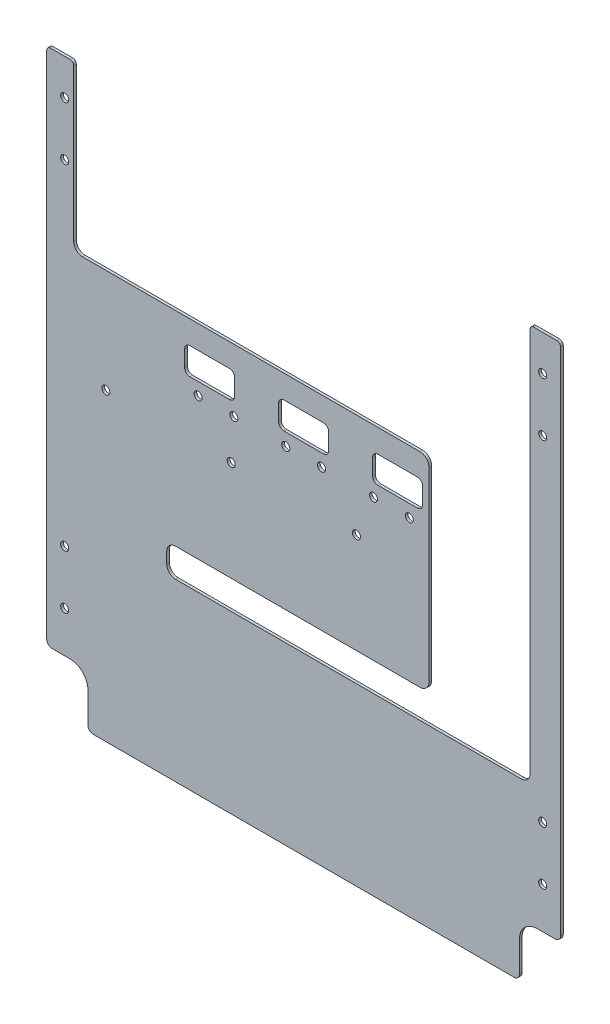
SolidWorks part; units mm, degrees
material "1023 Tôle d'acier au carbone (SS)"
ref_plane "Front" through (0, 0, 0) normal (0, 0, 1) x (1, 0, 0)
ref_plane "Top" through (0, 0, 0) normal (0, 1, 0) x (1, 0, 0)
ref_plane "Right" through (0, 0, 0) normal (1, 0, 0) x (0, 0, -1)
sketch "Esquisse1" plane through (0, 0, 0) normal (0, 0, 1) x (1, 0, 0)
  line L1 (0, 0) -> (287, 0)
  line L2 (0, 0) -> (0, 320)
  line L3 (0, 320) -> (287, 320)
  line L4 (287, 0) -> (287, 320)
  dimension "D1" = 287
  dimension "D2" = 320
extrude "Boss.-Extru.1" add sketch "Esquisse1" along normal blind 1.5
sketch "Esquisse2" plane through (0, 0, 1.5) normal (0, 0, 1) x (1, 0, 0)
  line L0 (143.5, 0) -> (143.5, 56.1801) construction
  line L1 (287, 0) -> (264, 0)
  line L2 (287, 0) -> (287, 30)
  line L3 (287, 30) -> (264, 30)
  line L4 (264, 0) -> (264, 30)
  line L5 (0, 0) -> (287, 0) construction
  line L6 (23, 0) -> (23, 30)
  line L7 (0, 30) -> (23, 30)
  line L8 (0, 0) -> (0, 30)
  line L9 (0, 0) -> (23, 0)
  dimension "D1" = 23
  dimension "D2" = 30
extrude "Enlèv. mat.-Extru.1" cut sketch "Esquisse2" against normal through all both and the other way through all
fillet "Congé1" radius 10 2 edges at (264, 30, 0.75) (23, 30, 0.75)
fillet "Congé2" radius 3 4 edges at (287, 30, 0.75) (0, 30, 0.75) (23, 0, 0.75) (264, 0, 0.75)
sketch "Esquisse3" plane through (0, 0, 1.5) normal (0, 0, 1) x (1, 0, 0)
  line L0 (287, 320) -> (0, 320) construction
  line L1 (73.5, 320) -> (213.5, 320)
  line L2 (73.5, 320) -> (73.5, 228)
  line L3 (73.5, 228) -> (213.5, 228)
  line L4 (213.5, 320) -> (213.5, 228)
  line L5 (143.5, 228) -> (143.5, 0) construction
  line L6 (26, 0) -> (261, 0) construction
  dimension "D1" = 140
  dimension "D2" = 92
extrude "Enlèv. mat.-Extru.2" cut sketch "Esquisse3" against normal through all both and the other way through all
sketch "Esquisse4" plane through (0, 0, 1.5) normal (0, 0, 1) x (1, 0, 0)
  line L0 (287, 320) -> (213.5, 320) construction
  line L1 (213.5, 320) -> (270, 320)
  line L2 (213.5, 320) -> (213.5, 98)
  line L3 (213.5, 98) -> (270, 98)
  line L4 (270, 320) -> (270, 98)
  line L5 (287, 33) -> (287, 320) construction
  line L6 (213.5, 320) -> (213.5, 228) construction
  line L7 (26, 0) -> (261, 0) construction
  dimension "D1" = 17
  dimension "D2" = 98
extrude "Enlèv. mat.-Extru.3" cut sketch "Esquisse4" against normal through all both and the other way through all
sketch "Esquisse5" plane through (0, 0, 1.5) normal (0, 0, 1) x (1, 0, 0)
  line L0 (73.5, 320) -> (0, 320) construction
  line L1 (73.5, 228) -> (15, 228)
  line L2 (73.5, 228) -> (73.5, 320)
  line L3 (73.5, 320) -> (15, 320)
  line L4 (15, 228) -> (15, 320)
  line L5 (0, 320) -> (0, 33) construction
  dimension "D1" = 15
extrude "Enlèv. mat.-Extru.4" cut sketch "Esquisse5" against normal through all both and the other way through all
sketch "Esquisse6" plane through (0, 0, 1.5) normal (0, 0, 1) x (1, 0, 0)
  line L0 (213.5, 98) -> (213.5, 228) construction
  line L1 (213.5, 98) -> (67, 98)
  line L2 (213.5, 98) -> (213.5, 114)
  line L3 (213.5, 114) -> (67, 114)
  line L4 (67, 98) -> (67, 114)
  line L5 (26, 0) -> (261, 0) construction
  line L6 (0, 320) -> (0, 33) construction
  dimension "D1" = 16
  dimension "D2" = 98
  dimension "D3" = 67
extrude "Enlèv. mat.-Extru.5" cut sketch "Esquisse6" against normal through all both and the other way through all
fillet "Congé3" radius 5 6 edges at (270, 98, 0.75) (67, 98, 0.75) (67, 114, 0.75) (213.5, 114, 0.75) (213.5, 228, 0.75) (15, 228, 0.75)
sketch "Esquisse7" plane through (0, 0, 1.5) normal (0, 0, 1) x (1, 0, 0)
  line L0 (277, 320) -> (277, 300) construction
  line L1 (287, 320) -> (270, 320) construction
  line L2 (270, 320) -> (270, 103) construction
  line L3 (277, 300) -> (277, 270) construction
  line L4 (143.5, 0) -> (143.5, 300) construction
  line L5 (26, 0) -> (261, 0) construction
  line L6 (10, 300) -> (10, 270) construction
  line L7 (10, 320) -> (10, 300) construction
  line L8 (0, 176.5) -> (287, 176.5) construction
  line L9 (0, 320) -> (0, 33) construction
  line L10 (287, 33) -> (287, 320) construction
  line L11 (277, 53) -> (277, 83) construction
  line L12 (277, 33) -> (277, 53) construction
  line L13 (10, 33) -> (10, 53) construction
  line L14 (10, 53) -> (10, 83) construction
  line L15 (33, 170) -> (0, 170) construction
  line L16 (33, 170) -> (103, 170) construction
  line L17 (103, 170) -> (103, 182.3786) construction
  circle A0 centre (277, 300) radius 2.25
  circle A1 centre (277, 270) radius 2.25
  circle A2 centre (10, 270) radius 2.25
  circle A3 centre (10, 300) radius 2.25
  circle A4 centre (277, 83) radius 2.25
  circle A5 centre (277, 53) radius 2.25
  circle A6 centre (10, 53) radius 2.25
  circle A7 centre (10, 83) radius 2.25
  circle A8 centre (33, 170) radius 2.25
  circle A9 centre (103, 170) radius 2.25
  circle A10 centre (173, 170) radius 2.25
  dimension "D2" = 4.5
  dimension "D4" = 30
  dimension "D6" = 33
  dimension "D1" = 7
  dimension "D3" = 20
  dimension "D5" = 70
  dimension "D7" = 170
extrude "Enlèv. mat.-Extru.6" cut sketch "Esquisse7" against normal through all both and the other way through all
sketch "Esquisse8" plane through (0, 0, 1.5) normal (0, 0, 1) x (1, 0, 0)
  line L0 (143.5, 0) -> (143.5, 158.346) construction
  line L1 (26, 0) -> (261, 0) construction
  line L2 (208.5, 228) -> (20, 228) construction
  line L3 (182.5, 193) -> (202.5, 193) construction
  line L4 (153.5, 193) -> (182.5, 193) construction
  line L5 (104.5, 193) -> (84.5, 193) construction
  circle A0 centre (133.5, 193) radius 2.25
  circle A1 centre (153.5, 193) radius 2.25
  circle A2 centre (182.5, 193) radius 2.25
  circle A3 centre (202.5, 193) radius 2.25
  circle A4 centre (84.5, 193) radius 2.25
  circle A5 centre (104.5, 193) radius 2.25
  dimension "D1" = 4.5
  dimension "D2" = 20
  dimension "D3" = 35
  dimension "D4" = 20
  dimension "D5" = 39
extrude "Enlèv. mat.-Extru.7" cut sketch "Esquisse8" against normal through all both and the other way through all
sketch "Esquisse9" plane through (0, 0, 1.5) normal (0, 0, 1) x (1, 0, 0)
  line L0 (133.5, 193) -> (153.5, 193) construction
  line L1 (129.5, 215) -> (157.5, 215)
  line L2 (129.5, 215) -> (129.5, 200)
  line L3 (129.5, 200) -> (157.5, 200)
  line L4 (157.5, 215) -> (157.5, 200)
  line L5 (143.5, 193) -> (143.5, 215) construction
  line L6 (153.5, 193) -> (169.75, 193) construction
  line L7 (169.75, 193) -> (169.75, 205) construction
  line L8 (182, 215) -> (182, 200)
  line L9 (210, 200) -> (182, 200)
  line L10 (210, 215) -> (210, 200)
  line L11 (210, 215) -> (182, 215)
  line L12 (182.5, 193) -> (182.5, 194.1597) construction
  line L13 (104.5, 193) -> (104.5, 194.1597) construction
  line L14 (77, 215) -> (105, 215)
  line L15 (77, 215) -> (77, 200)
  line L16 (77, 200) -> (105, 200)
  line L17 (105, 215) -> (105, 200)
  dimension "D1" = 28
  dimension "D2" = 15
  dimension "D3" = 22
  dimension "D4" = 27.5
extrude "Enlèv. mat.-Extru.8" cut sketch "Esquisse9" against normal through all both and the other way through all
fillet "Congé4" radius 3 12 edges at (157.5, 200, 0.75) (157.5, 215, 0.75) (129.5, 215, 0.75) (129.5, 200, 0.75) (210, 200, 0.75) (210, 215, 0.75) (182, 215, 0.75) (182, 200, 0.75) (105, 200, 0.75) (105, 215, 0.75) (77, 215, 0.75) (77, 200, 0.75)
fillet "Congé6" radius 2 4 edges at (287, 320, 0.75) (270, 320, 0.75) (0, 320, 0.75) (15, 320, 0.75)
